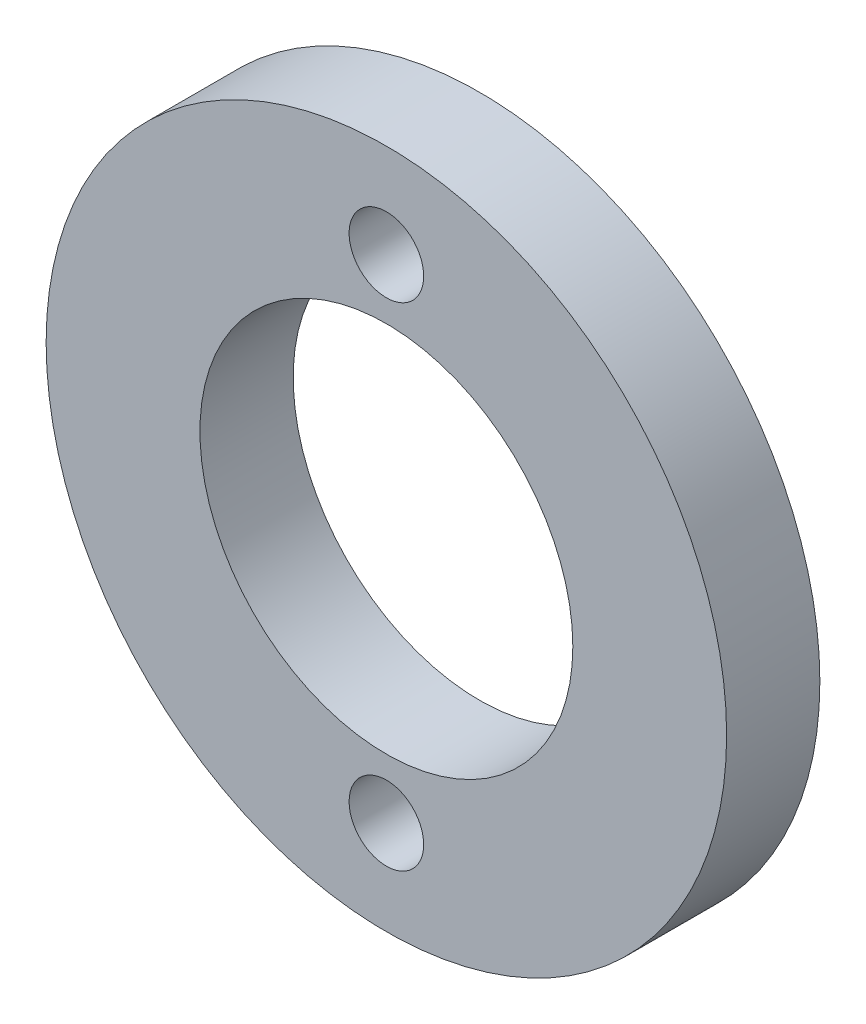
SolidWorks part; units mm, degrees
material "PA Type 6"
ref_plane "Front" through (0, 0, 0) normal (0, 0, 1) x (1, 0, 0)
ref_plane "Top" through (0, 0, 0) normal (0, 1, 0) x (1, 0, 0)
ref_plane "Right" through (0, 0, 0) normal (1, 0, 0) x (0, 0, -1)
sketch "Sketch1" plane through (0, 0, 0) normal (0, 0, 1) x (1, 0, 0)
  line L0 (0, 23.8598) -> (0, -24.6334) construction
  line L1 (-27.6594, 0) -> (23.6863, 0) construction
  circle A0 centre (0, 0) radius 18.25
  circle A1 centre (0, 0) radius 13.2 construction
  circle A2 centre (0, 13.2) radius 2
  circle A3 centre (0, -13.2) radius 2
  circle A4 centre (0, 0) radius 10
  dimension "D1" = 36.5
  dimension "D2" = 26.4
  dimension "D3" = 4
  dimension "D4" = 20
extrude "Boss-Extrude1" add sketch "Sketch1" along normal blind 5
